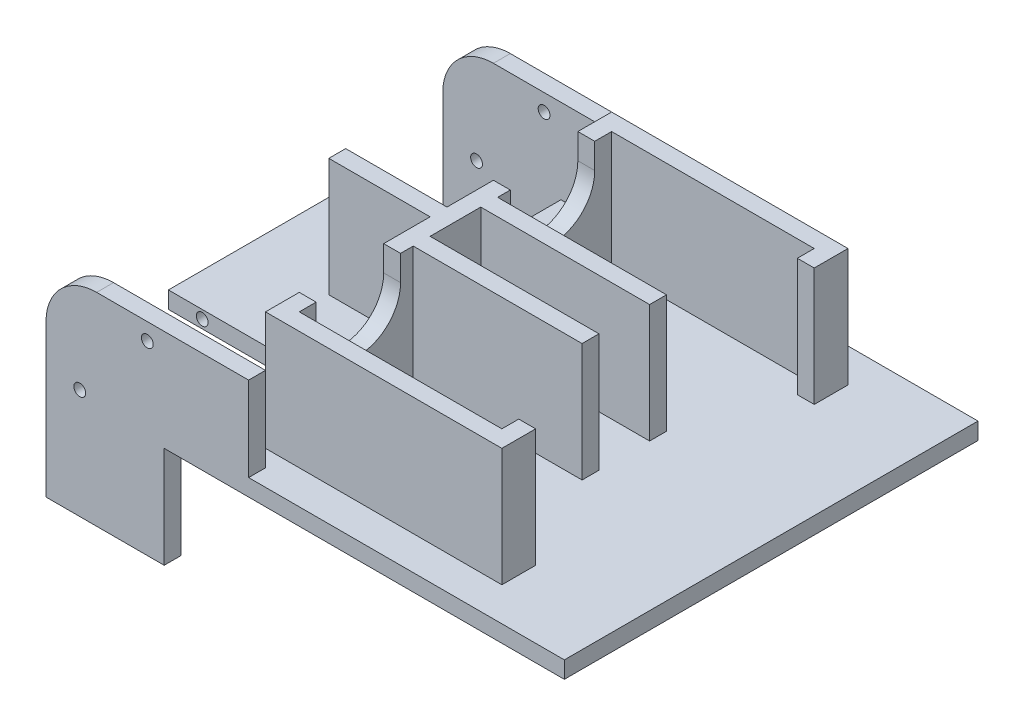
SolidWorks part; units mm, degrees
ref_plane "Front" through (0, 0, 0) normal (0, 0, 1) x (1, 0, 0)
ref_plane "Top" through (0, 0, 0) normal (0, 1, 0) x (1, 0, 0)
ref_plane "Right" through (0, 0, 0) normal (1, 0, 0) x (0, 0, -1)
sketch "草图1" plane through (0, 0, 0) normal (0, 1, 0) x (1, 0, 0)
  line L0 (7.5, 15.2806) -> (7.5, -20.7687) construction
  line L1 (-12.5, 12.25) -> (11.2, 12.25)
  line L2 (-12.5, 11.25) -> (-12.5, 5)
  line L3 (-12.5, -12.25) -> (11.2, -12.25)
  line L4 (11.2, 12.25) -> (11.2, -12.25)
  line L5 (-12.5, -12.25) -> (-19.5, -12.25)
  line L6 (-19.5, -12.25) -> (-19.5, -11.25)
  line L7 (-19.5, -11.25) -> (-12.5, -11.25)
  line L8 (0, 0) -> (-31.4338, 0) construction
  line L9 (-12.5, 12.25) -> (-19.5, 12.25)
  line L10 (-19.5, 12.25) -> (-19.5, 11.25)
  line L11 (-19.5, 11.25) -> (-12.5, 11.25)
  line L12 (-12.5, 5) -> (-19.5, 5)
  line L13 (-19.5, 5) -> (-19.5, -5)
  line L14 (-19.5, -5) -> (-12.5, -5)
  line L15 (-12.5, -5) -> (-12.5, -11.25)
  point P7 (7.5, 9)
  point P8 (7.5, -9)
  point P23 (-17.5, 5)
  point P26 (-19.5, 3)
  dimension "D15" = 10
  dimension "D1" = 23.7
  dimension "D2" = 24.5
  dimension "D3" = 12.5
  dimension "D4" = 5
  dimension "D5" = 9
  dimension "D6" = 9
  dimension "D9" = 20
  dimension "D10" = 7
  dimension "D11" = 1
  dimension "D13" = 2
  dimension "D14" = 2
extrude "凸台-拉伸1" add sketch "草图1" along normal blind 1
sketch "草图2" plane through (0, 0, 0) normal (0, -1, 0) x (1, 0, 0)
  line L0 (11.2, -12.25) -> (-19.5, -12.25) construction
  line L1 (-19.5, 12.25) -> (-12.5, 12.25)
  line L2 (-19.5, 12.25) -> (-19.5, 11.25)
  line L3 (-19.5, 11.25) -> (-12.5, 11.25)
  line L4 (-12.5, 12.25) -> (-12.5, 11.25)
  line L9 (-19.5, -11.25) -> (-12.5, -11.25)
  line L10 (-19.5, -11.25) -> (-19.5, -12.25)
  line L11 (-19.5, -12.25) -> (-12.5, -12.25)
  line L12 (-12.5, -11.25) -> (-12.5, -12.25)
extrude "凸台-拉伸2" add sketch "草图2" along normal blind 6 and the other way blind 6
fillet "圆角1" radius 3 2 edges at (-19.5, 6, 11.75) (-19.5, 6, -11.75)
sketch "草图3" plane through (0, 0, 12.25) normal (0, 0, 1) x (1, 0, 0)
  line L0 (-19.5, 3) -> (-19.5, -6) construction
  line L2 (-12.5, 0) -> (11.2, 0) construction
  line L3 (-12.5, 1) -> (11.2, 1) construction
  line L4 (-12.5, 6) -> (-12.5, 1) construction
  circle A0 centre (-17.5, 0.5) radius 0.35
  circle A1 centre (-13.5, 5) radius 0.35
  point P0 (-17.5, 0.5)
  point P7 (-13.5, 5)
  dimension "D3" = 0.7
  dimension "D6" = 0.7
  dimension "D1" = 2
  dimension "D2" = 0.5
  dimension "D4" = 4
  dimension "D5" = 1
extrude "切除-拉伸1" cut sketch "草图3" against normal through all
sketch "草图4" plane through (-12.5, 0, 0) normal (1, 0, 0) x (0, 0, -1)
  line L1 (-12.25, 6) -> (-11.25, 6)
  line L2 (-12.25, 6) -> (-12.25, 1)
  line L3 (-12.25, 1) -> (-11.25, 1)
  line L4 (-11.25, 6) -> (-11.25, 1)
  line L5 (11.25, 6) -> (12.25, 6)
  line L6 (11.25, 6) -> (11.25, 1)
  line L7 (11.25, 1) -> (12.25, 1)
  line L8 (12.25, 6) -> (12.25, 1)
extrude "凸台-拉伸3" add sketch "草图4" along normal blind 5
sketch "草图5" plane through (0, 1, 0) normal (0, 1, 0) x (1, 0, 0)
  line L0 (-8.5, -8.25) -> (-8.5, -10.25)
  line L5 (-8.5, -10.25) -> (5.5, -10.25)
  line L6 (5.5, -10.25) -> (5.5, -8.25)
  line L7 (5.5, -8.25) -> (4.5, -8.25)
  line L8 (4.5, -8.25) -> (4.5, -9.25)
  line L9 (4.5, -9.25) -> (-7.5, -9.25)
  line L10 (-7.5, -9.25) -> (-7.5, -8.25)
  line L13 (-7.5, -12.25) -> (-7.5, -11.25) construction
  line L14 (-7.5, -12.25) -> (11.2, -12.25) construction
  line L30 (-7.5, -1.5) -> (-7.5, 1.5)
  line L31 (-14.5, -0.5) -> (-8.5, -0.5)
  line L32 (-8.5, -0.5) -> (-8.5, -3.5)
  line L34 (-7.5, -3.5) -> (-7.5, -2.5)
  line L35 (-7.5, -2.5) -> (2.5, -2.5)
  line L36 (2.5, -2.5) -> (2.5, -1.5)
  line L37 (2.5, -1.5) -> (-7.5, -1.5)
  line L38 (-7.5, 1.5) -> (2.5, 1.5)
  line L39 (2.5, 1.5) -> (2.5, 2.5)
  line L40 (2.5, 2.5) -> (-7.5, 2.5)
  line L41 (-7.5, 2.5) -> (-7.5, 3.5)
  line L43 (-8.5, 3.7424) -> (-8.5, 0.5)
  line L44 (-8.5, 0.5) -> (-14.5, 0.5)
  line L45 (-14.5, 0.5) -> (-14.5, -0.5)
  line L46 (0, 0) -> (18.8872, 0) construction
  line L47 (4.5, 8.25) -> (4.5, 9.25)
  line L48 (5.5, 8.25) -> (4.5, 8.25)
  line L49 (5.5, 10.25) -> (5.5, 8.25)
  line L50 (-8.5, 10.25) -> (5.5, 10.25)
  line L51 (-8.5, 8.25) -> (-8.5, 10.25)
  line L53 (-7.5, 9.25) -> (-7.5, 8.25)
  line L54 (4.5, 9.25) -> (-7.5, 9.25)
  line L55 (-7.5, -3.5) -> (-7.5, -8.25)
  line L56 (-8.5, -3.5) -> (-8.5, -8.25)
  line L57 (-7.5, 8.25) -> (-7.5, 3.5)
  line L58 (-8.5, 8.25) -> (-8.5, 3.7424)
  line L60 (-19.5, -5) -> (-12.5, -5) construction
  dimension "D1" = 14
  dimension "D2" = 12
  dimension "D3" = 1
  dimension "D4" = 1
  dimension "D5" = 1
  dimension "D6" = 1
  dimension "D7" = 0
  dimension "D8" = 2
  dimension "D9" = 6
  dimension "D10" = 0
  dimension "D11" = 1
  dimension "D12" = 10
  dimension "D13" = 1
  dimension "D14" = 1
  dimension "D15" = 10
  dimension "D16" = 1
  dimension "D17" = 1
  dimension "D19" = 10
  dimension "D20" = 3
  dimension "D21" = 3
  dimension "D22" = 1
  dimension "D23" = 1
  dimension "D24" = 4.5
extrude "凸台-拉伸4" add sketch "草图5" along normal blind 7
sketch "草图6" plane through (-8.5, 0, 0) normal (-1, 0, 0) x (0, 0, 1)
  line L1 (-10.25, 8) -> (-0.5, 8) construction
  line L2 (0.5, 8) -> (10.25, 8) construction
  line L3 (-8.25, 6.5) -> (-8.25, 9.6215)
  line L4 (-8.25, 9.6215) -> (-3.25, 9.6215)
  line L5 (-3.25, 9.6215) -> (-3.25, 6.5)
  line L6 (3.25, 6.5) -> (3.25, 9.8302)
  line L7 (3.25, 9.8302) -> (8.25, 9.8302)
  line L8 (8.25, 9.8302) -> (8.25, 6.5)
  line L11 (-10.25, 8) -> (-10.25, 1) construction
  line L13 (10.25, 8) -> (10.25, 1) construction
  arc A0 (-8.25, 6.5) -> (-3.25, 6.5) centre (-5.75, 6.5) ccw
  arc A1 (3.25, 6.5) -> (8.25, 6.5) centre (5.75, 6.5) ccw
  point P0 (-5.75, 6.5)
  point P1 (5.75, 6.5)
  dimension "D1" = 5
  dimension "D2" = 5
  dimension "D3" = 1.5
  dimension "D4" = 1.5
  dimension "D5" = 4.5
  dimension "D6" = 4.5
extrude "切除-拉伸2" cut sketch "草图6" against normal blind 7
